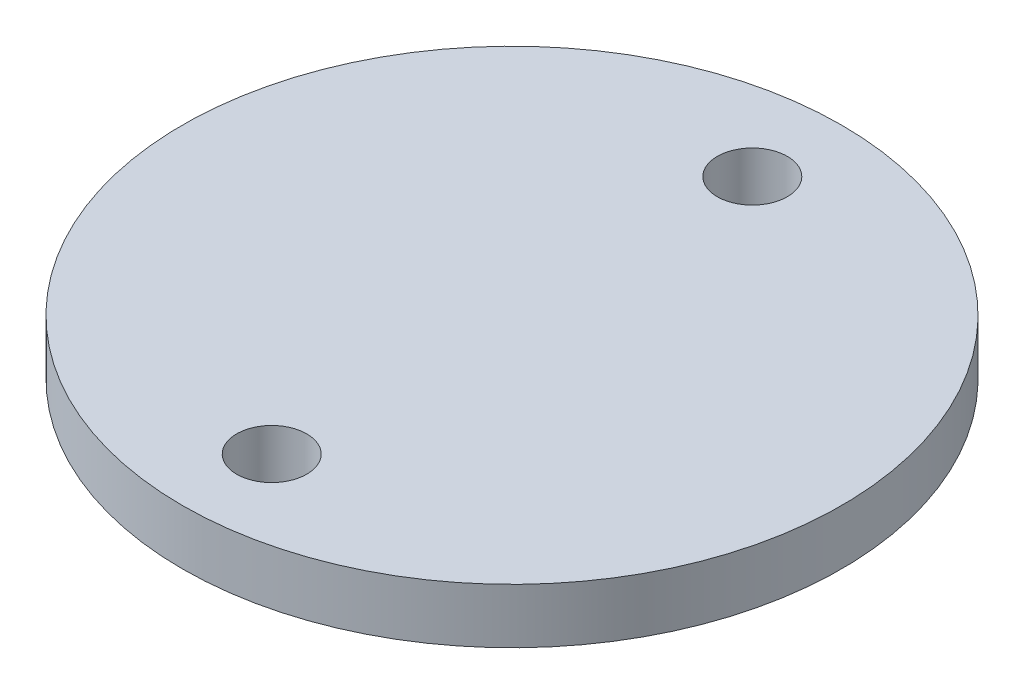
SolidWorks part; units mm, degrees
ref_plane "Front Plane" through (0, 0, 0) normal (0, 0, 1) x (1, 0, 0)
ref_plane "Top Plane" through (0, 0, 0) normal (0, 1, 0) x (1, 0, 0)
ref_plane "Right Plane" through (0, 0, 0) normal (1, 0, 0) x (0, 0, -1)
sketch "Sketch1" plane through (0, 0, 0) normal (0, 1, 0) x (1, 0, 0)
  circle A0 centre (0, 0) radius 30.48
  dimension "D1" = 60.96
extrude "Boss-Extrude1" add sketch "Sketch1" along normal blind 5.08
sketch "Sketch2" plane through (0, 5.08, 0) normal (0, 1, 0) x (1, 0, 0)
  line L0 (0, 22.225) -> (0, -22.225) construction
  circle A1 centre (0, 22.225) radius 3.2385
  circle A2 centre (0, -22.225) radius 3.2385
  point P1 (0, 0)
  dimension "D2" = 6.477
  dimension "D1" = 44.45
extrude "Cut-Extrude1" cut sketch "Sketch2" against normal through all
